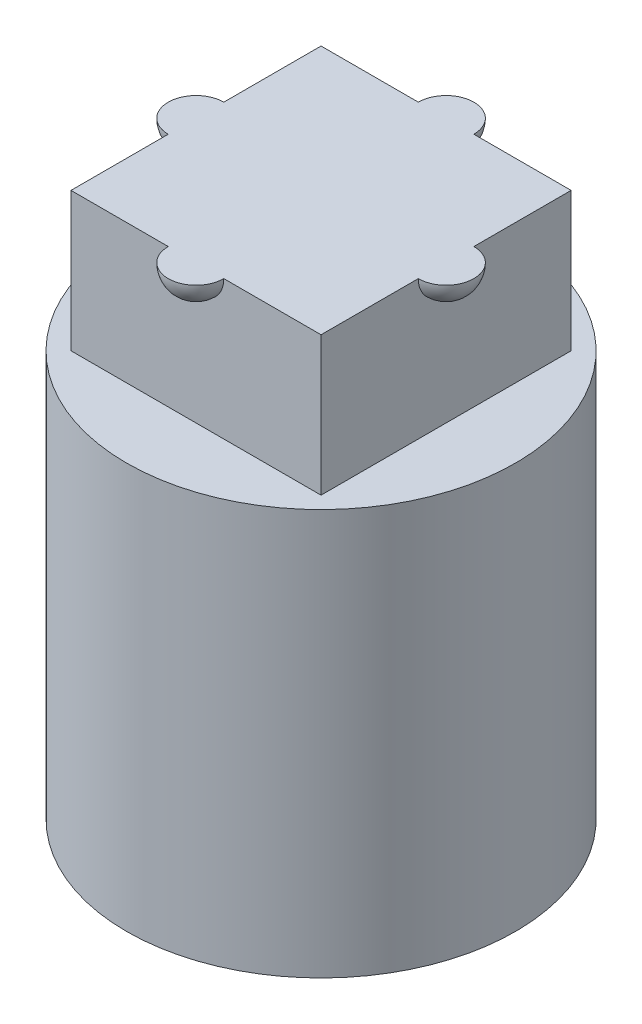
SolidWorks part; units mm, degrees
ref_plane "前视基准面" through (0, 0, 0) normal (0, 0, 1) x (1, 0, 0)
ref_plane "上视基准面" through (0, 0, 0) normal (0, 1, 0) x (1, 0, 0)
ref_plane "右视基准面" through (0, 0, 0) normal (1, 0, 0) x (0, 0, -1)
sketch "草图1" plane through (0, 0, 0) normal (0, 1, 0) x (1, 0, 0)
  line L1 (0.95, -1.2) -> (-0.95, -1.2)
  line L2 (1.2, -0.95) -> (1.2, 0.95)
  line L3 (0.95, 1.2) -> (-0.95, 1.2)
  line L4 (-1.2, -0.95) -> (-1.2, 0.95)
  circle A0 centre (0, 0) radius 3.5
  arc A1 (1.2, 0.95) -> (0.95, 1.2) centre (1.2, 1.2) ccw
  arc A2 (-0.95, 1.2) -> (-1.2, 0.95) centre (-1.2, 1.2) ccw
  arc A3 (-1.2, -0.95) -> (-0.95, -1.2) centre (-1.2, -1.2) ccw
  arc A4 (0.95, -1.2) -> (1.2, -0.95) centre (1.2, -1.2) ccw
  dimension "D1" = 2.4
  dimension "D4" = 0.5
  dimension "D5" = 0.5
  dimension "D6" = 0.5
  dimension "D3" = 0.5
  dimension "D2" = 2.4
extrude "凸台-拉伸1" add sketch "草图1" along normal blind 4
sketch "草图3" plane through (0, 4, 0) normal (0, 1, 0) x (1, 0, 0)
  circle A2 centre (0, 0) radius 3.5
  circle A3 centre (0, 0) radius 3.5
  dimension "D1" = 0
extrude "凸台-拉伸2" add sketch "草图3" along normal blind 3.3
sketch "草图4" plane through (0, 7.3, 0) normal (0, 1, 0) x (1, 0, 0)
  line L1 (-2.25, 2.25) -> (2.25, 2.25)
  line L2 (-2.25, 2.25) -> (-2.25, -2.25)
  line L3 (-2.25, -2.25) -> (2.25, -2.25)
  line L4 (2.25, 2.25) -> (2.25, -2.25)
  line L5 (-2.25, 2.25) -> (2.25, -2.25) construction
  line L6 (-2.25, -2.25) -> (2.25, 2.25) construction
  point P0 (0, 0)
  dimension "D1" = 4.5
  dimension "D2" = 4.5
extrude "凸台-拉伸3" add sketch "草图4" along normal blind 2.5
sketch "草图5" plane through (0, 9.8, 0) normal (0, 1, 0) x (1, 0, 0)
  line L0 (-2.25, 2.25) -> (-2.25, -2.25) construction
  line L1 (2.25, -2.25) -> (2.25, 2.25) construction
  line L2 (-2.75, 0) -> (-1.75, 0)
  line L3 (1.75, 0) -> (2.75, 0)
  arc A0 (-2.75, 0) -> (-1.75, 0) centre (-2.25, 0) ccw
  arc A1 (1.75, 0) -> (2.75, 0) centre (2.25, 0) ccw
  dimension "D1" = 1
  dimension "D2" = 1
revolve "旋转1" add sketch "草图5" angle 360 about L2
sketch "草图6" plane through (0, 9.8, 0) normal (0, 1, 0) x (1, 0, 0)
  line L0 (-2.25, -2.25) -> (2.25, -2.25) construction
  line L1 (2.25, 2.25) -> (-2.25, 2.25) construction
  line L2 (0, -2.75) -> (0, -1.75)
  line L3 (0, 1.75) -> (0, 2.75)
  arc A0 (0, -1.75) -> (0, -2.75) centre (0, -2.25) ccw
  arc A1 (0, 2.75) -> (0, 1.75) centre (0, 2.25) ccw
  dimension "D1" = 1
  dimension "D2" = 1
revolve "旋转2" add sketch "草图6" angle 360 about L2
sketch "草图7" plane through (0, 9.8, 0) normal (0, 1, 0) x (1, 0, 0)
  circle A0 centre (0, 0) radius 3.5
extrude "切除-拉伸1" cut sketch "草图7" along normal blind 10
